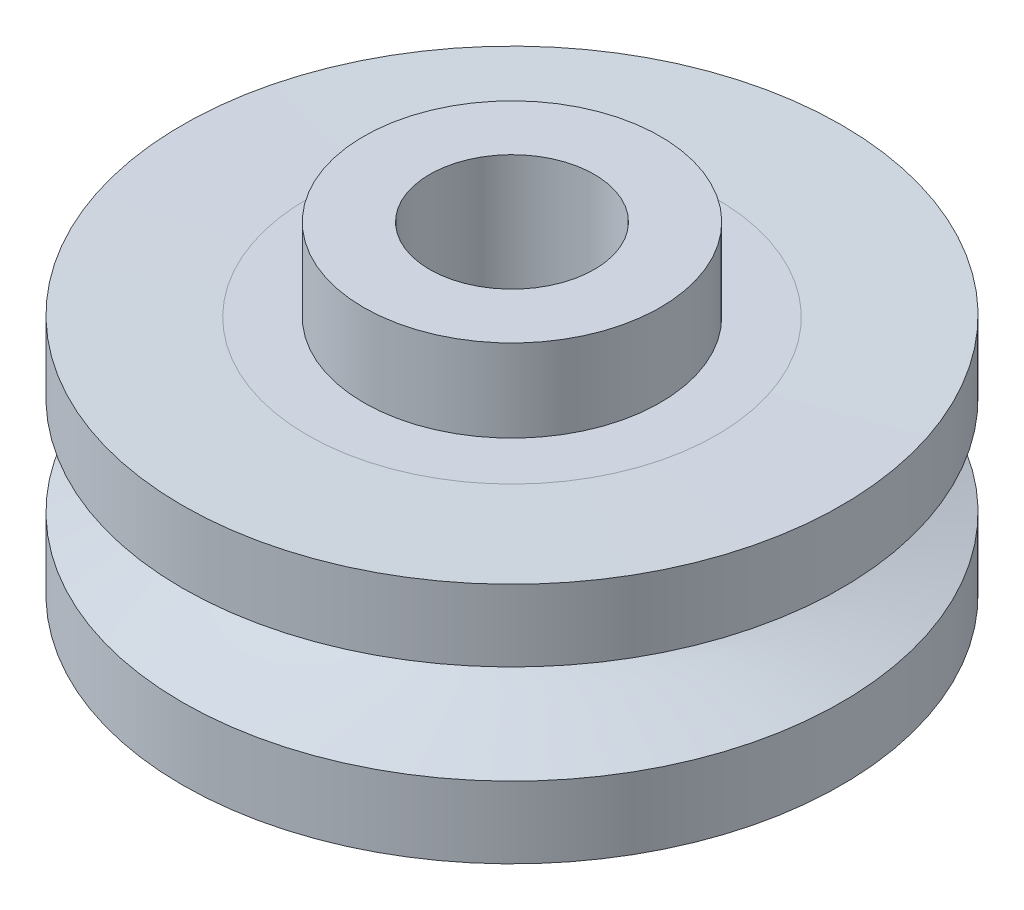
SolidWorks part; units mm, degrees
ref_plane "前视基准面" through (0, 0, 0) normal (0, 0, 1) x (1, 0, 0)
ref_plane "上视基准面" through (0, 0, 0) normal (0, 1, 0) x (1, 0, 0)
ref_plane "右视基准面" through (0, 0, 0) normal (1, 0, 0) x (0, 0, -1)
sketch "草图1" plane through (0, 0, 0) normal (0, 0, 1) x (1, 0, 0)
  line L0 (0, 2.0786) -> (0, -2.1269) construction
  line L1 (1.8, -1.45) -> (2.4831, -1.45)
  line L2 (1, 0) -> (5.9554, 0) construction
  line L3 (1, 2.45) -> (1, -2.45)
  line L4 (1.8, -2.45) -> (1.8, -1.45)
  line L5 (4, 1.4695) -> (4, 0.6)
  line L6 (1, -2.45) -> (1.8, -2.45)
  line L7 (2.4831, -1.45) -> (4, -1.4695)
  line L8 (2.4831, 1.45) -> (4, 1.4695)
  line L9 (4, -1.4695) -> (4, -0.6)
  line L11 (1, 2.45) -> (1.8, 2.45)
  line L12 (1.8, 2.45) -> (1.8, 1.45)
  line L13 (1.8, 1.45) -> (2.4831, 1.45)
  conic Q0 (4, 0.6) -> (4, -0.6) control (2.3307, 0) rho 0.719596
  point P14 (0, 2)
  dimension "D1" = 1
  dimension "D2" = 3
  dimension "D3" = 2.45
  dimension "D4" = 1.2
revolve "旋转9" add sketch "草图1" angle 360 about L0
